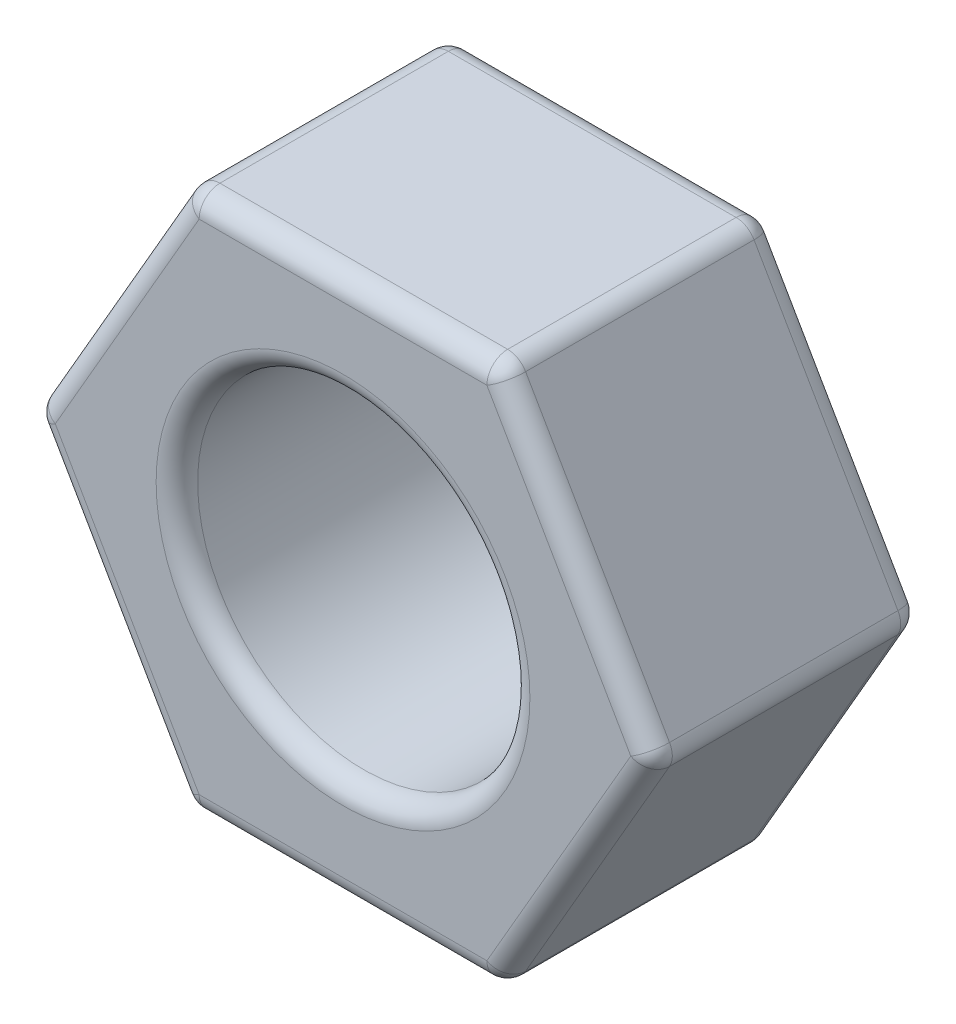
SolidWorks part; units mm, degrees
material "Cast Alloy Steel"
ref_plane "Front Plane" through (0, 0, 0) normal (0, 0, 1) x (1, 0, 0)
ref_plane "Top Plane" through (0, 0, 0) normal (0, 1, 0) x (1, 0, 0)
ref_plane "Right Plane" through (0, 0, 0) normal (1, 0, 0) x (0, 0, -1)
sketch "Sketch1" plane through (0, 0, 0) normal (0, 0, 1) x (1, 0, 0)
  line L1 (-7.5056, 0) -> (-3.7528, -6.5)
  line L2 (-3.7528, -6.5) -> (3.7528, -6.5)
  line L3 (3.7528, -6.5) -> (7.5056, 0)
  line L4 (7.5056, 0) -> (3.7528, 6.5)
  line L5 (3.7528, 6.5) -> (-3.7528, 6.5)
  line L6 (-3.7528, 6.5) -> (-7.5056, 0)
  circle A0 centre (0, 0) radius 6.5 construction
extrude "Boss-Extrude1" add sketch "Sketch1" along normal blind 6.5
hole_wizard "M7 Clearance Hole1" positions "Sketch2" profile "Sketch3" hole size "M7" standard "ANSI Metric"
sketch "Sketch2" plane through (0, 0, 6.5) normal (0, 0, 1) x (1, 0, 0)
  point P0 (0, 0)
sketch "Sketch3" plane through (0, 0, 6.5) normal (1, 0, 0) x (0, -1, 0)
  line L0 (0, 0) -> (0, 16.4034)
  line L1 (0, 16.4034) -> (4, 14)
  line L2 (4, 14) -> (4, 0)
  line L5 (4, 0) -> (0, 0)
  line L10 (0, 16.4034) -> (-4, 14) construction
  line L11 (0, -6.35) -> (0, 107.95) construction
  dimension "Hole Dia." = 8
  dimension "Hole Depth" = 14
  dimension "Drill Angle" = 118
fillet "Fillet1" radius 0.5 20 edges at (4, 0, 6.5) (4, 0, 0) (-3.7528, -6.5, 3.25) (3.7528, -6.5, 3.25) (7.5056, 0, 3.25) (-7.5056, 0, 3.25) (-3.7528, 6.5, 3.25) (3.7528, 6.5, 3.25) (5.6292, 3.25, 0) (5.6292, -3.25, 0) (0, -6.5, 0) (-5.6292, -3.25, 0) (-5.6292, 3.25, 0) (0, 6.5, 0) (5.6292, 3.25, 6.5) (5.6292, -3.25, 6.5) (0, -6.5, 6.5) (-5.6292, -3.25, 6.5) (-5.6292, 3.25, 6.5) (0, 6.5, 6.5)
